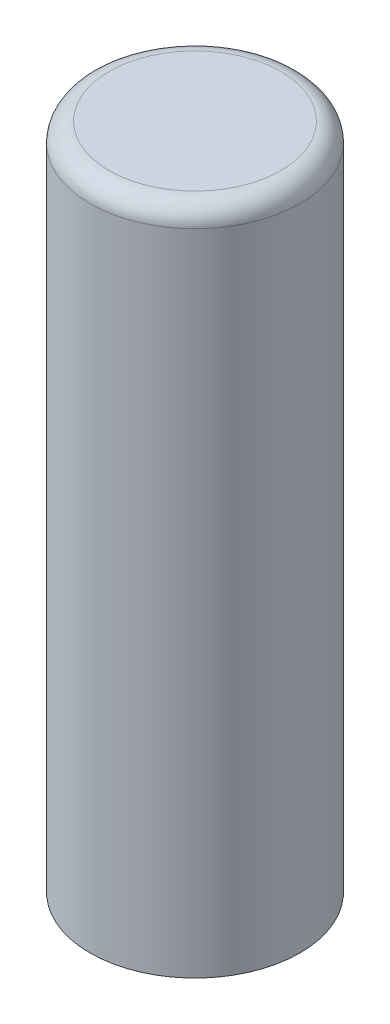
SolidWorks part; units mm, degrees
ref_plane "Front Plane" through (0, 0, 0) normal (0, 0, 1) x (1, 0, 0)
ref_plane "Top Plane" through (0, 0, 0) normal (0, 1, 0) x (1, 0, 0)
ref_plane "Right Plane" through (0, 0, 0) normal (1, 0, 0) x (0, 0, -1)
sketch "Sketch1" plane through (0, 0, 0) normal (0, 1, 0) x (1, 0, 0)
  circle A0 centre (0, 0) radius 3.4925
  dimension "D1" = 6.985
extrude "Boss-Extrude1" add sketch "Sketch1" along normal blind 22.225
fillet "Fillet1" radius 0.635 1 edges at (0, 22.225, 3.4925)
sketch "Sketch2" plane through (0, 0, 0) normal (0, -1, 0) x (1, 0, 0)
  circle A0 centre (0, 0) radius 1.778
  dimension "D1" = 3.556
extrude "Cut-Extrude1" cut sketch "Sketch2" against normal blind 8.255
